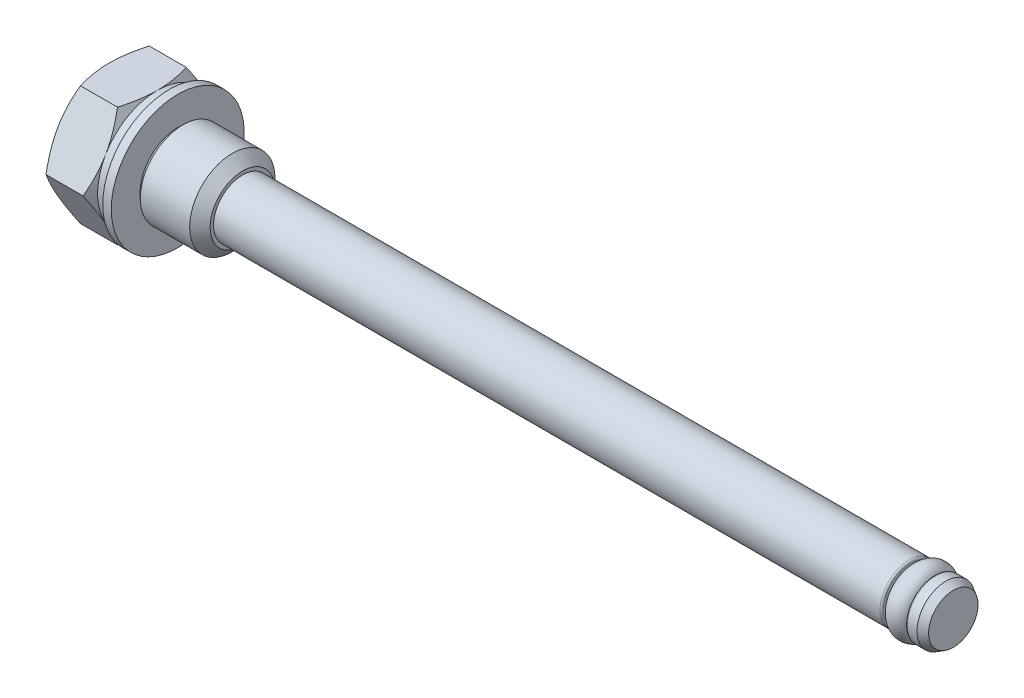
SolidWorks part; units mm, degrees
ref_plane "Front Plane" through (0, 0, 0) normal (0, 0, 1) x (1, 0, 0)
ref_plane "Top Plane" through (0, 0, 0) normal (0, 1, 0) x (1, 0, 0)
ref_plane "Right Plane" through (0, 0, 0) normal (1, 0, 0) x (0, 0, -1)
ref_plane "Plane1" through (0, 0, 0) normal (0, 0, 1) x (1, 0, 0)
sketch "Sketch1" plane through (0, 0, 0) normal (0, 0, 1) x (1, 0, 0)
  line L0 (-3.5, 0) -> (-3.5, 3.5)
  line L1 (-3.5, 3.5) -> (-2.1, 5.9249)
  line L2 (-2.1, 5.9249) -> (-0.7, 3.5)
  line L3 (-0.7, 3.5) -> (0, 3.5)
  line L4 (0, 3.5) -> (0, 2.5)
  line L5 (0, 2.5) -> (0.2586, 2.2414)
  line L6 (0.5414, 2.2414) -> (0.8, 2.5)
  line L7 (0.8, 2.5) -> (3.7, 2.5)
  line L8 (3.7, 2.5) -> (4.3, 1.9)
  line L9 (4.3, 1.9) -> (4.3, 1.7)
  line L10 (4.3, 1.7) -> (43.4, 1.7)
  line L11 (43.5, 1.6) -> (43.5, 1.3)
  line L12 (43.6, 1.2) -> (44.8, 1.2)
  line L13 (44.9, 1.3) -> (44.9, 1.6)
  line L14 (45, 1.7) -> (45.567, 1.7)
  line L15 (45.567, 1.7) -> (46, 1.45)
  line L16 (46, 1.45) -> (46, 0)
  line L17 (46, 0) -> (-3.5, 0)
  line L18 (46, 0) -> (-3.5, 0) construction
  arc A0 (0.2586, 2.2414) -> (0.5414, 2.2414) centre (0.4, 2.3828) ccw
  arc A1 (43.4, 1.7) -> (43.5, 1.6) centre (43.4, 1.6) cw
  arc A2 (43.5, 1.3) -> (43.6, 1.2) centre (43.6, 1.3) ccw
  arc A3 (44.8, 1.2) -> (44.9, 1.3) centre (44.8, 1.3) ccw
  arc A4 (44.9, 1.6) -> (45, 1.7) centre (45, 1.6) cw
revolve "Revolve1" add sketch "Sketch1" angle 360 about L18
cosmetic thread "Cosmetic Thread1" parameters "D1"=3.2065, "D2"=4.387
ref_plane "Plane2" through (-3.5, 0, 0) normal (-1, 0, 0) x (0, 0, 1)
sketch "Sketch2" plane through (-3.5, 0, 0) normal (-1, 0, 0) x (0, 0, 1)
  line L0 (-10, -10) -> (10, -10)
  line L1 (10, -10) -> (10, 10)
  line L2 (10, 10) -> (-10, 10)
  line L3 (-10, 10) -> (-10, -10)
  line L4 (2.0207, -3.5) -> (4.0415, 0)
  line L5 (4.0415, 0) -> (2.0207, 3.5)
  line L6 (2.0207, 3.5) -> (-2.0207, 3.5)
  line L7 (-2.0207, 3.5) -> (-4.0415, 0)
  line L8 (-4.0415, 0) -> (-2.0207, -3.5)
  line L9 (-2.0207, -3.5) -> (2.0207, -3.5)
extrude "Cut-Extrude1" cut sketch "Sketch2" against normal blind 5
ref_plane "Plane3" through (0, 0, 0) normal (0, 0, 1) x (1, 0, 0)
sketch "Sketch3" plane through (0, 0, 0) normal (0, 0, 1) x (1, 0, 0)
  line L0 (43.5, 1.2) -> (44.9, 1.2)
  line L1 (44.9, 0) -> (43.5, 0) construction
  arc A0 (44.9, 1.2) -> (43.5, 1.2) centre (44.2, 1.2) ccw
revolve "Revolve2" add sketch "Sketch3" angle 360 about L1
ref_plane "Plane4" through (0, 0, 0) normal (0, 0, 1) x (1, 0, 0)
sketch "Sketch4" plane through (0, 0, 0) normal (0, 0, 1) x (1, 0, 0)
  line L0 (0, 2.15) -> (0.5, 2.15)
  line L1 (0.5, 2.15) -> (0.5, 3.9)
  line L2 (0.5, 3.9) -> (0, 3.9)
  line L3 (0, 3.9) -> (0, 2.15)
  line L4 (0.5, 0) -> (0, 0) construction
revolve "Revolve3" add sketch "Sketch4" angle 360 about L4
